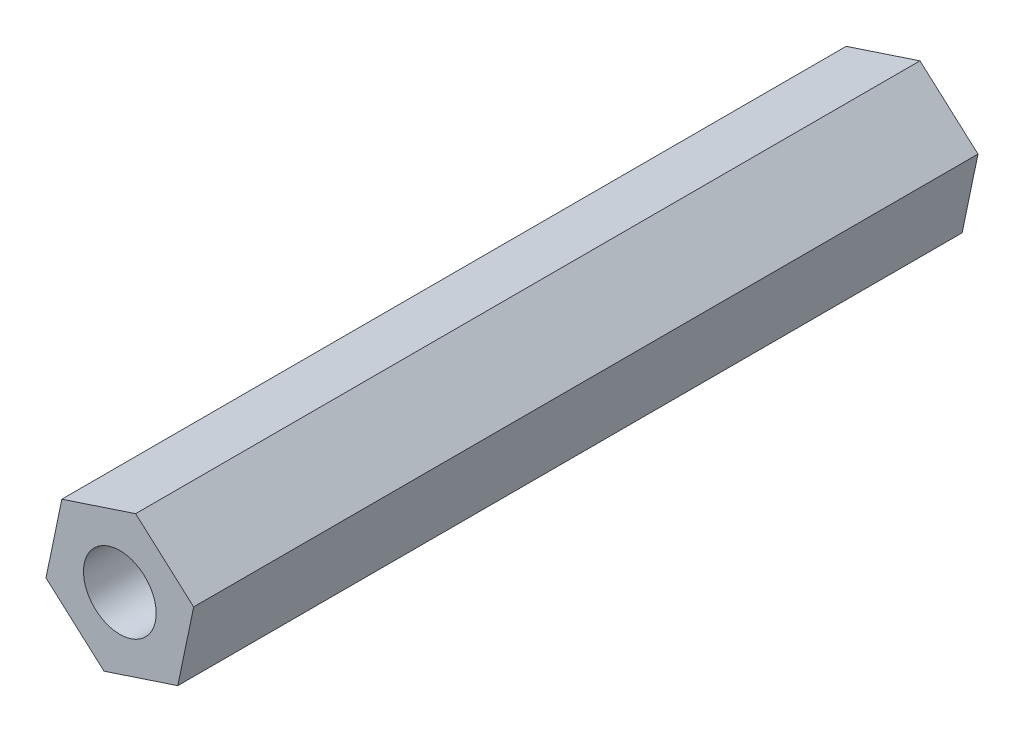
SolidWorks part; units mm, degrees
material "Latón"
ref_plane "Alzado" through (0, 0, 0) normal (0, 0, 1) x (1, 0, 0)
ref_plane "Planta" through (0, 0, 0) normal (0, 1, 0) x (1, 0, 0)
ref_plane "Vista lateral" through (0, 0, 0) normal (1, 0, 0) x (0, 0, -1)
sketch "Croquis1" plane through (0, 0, 0) normal (0, 0, 1) x (1, 0, 0)
  line L1 (3.454, 1.14) -> (0.7397, 3.5613)
  line L2 (0.7397, 3.5613) -> (-2.7143, 2.4213)
  line L3 (-2.7143, 2.4213) -> (-3.454, -1.14)
  line L4 (-3.454, -1.14) -> (-0.7397, -3.5613)
  line L5 (-0.7397, -3.5613) -> (2.7143, -2.4213)
  line L6 (2.7143, -2.4213) -> (3.454, 1.14)
  circle A0 centre (0, 0) radius 3.15 construction
  dimension "D1" = 6.3
extrude "Saliente-Extruir1" add sketch "Croquis1" along normal blind 36.7
sketch "Croquis2" plane through (0, 0, 36.7) normal (0, 0, 1) x (1, 0, 0)
  circle A0 centre (0, 0) radius 1.7
  dimension "D1" = 3.4
extrude "Cortar-Extruir1" cut sketch "Croquis2" against normal through all
